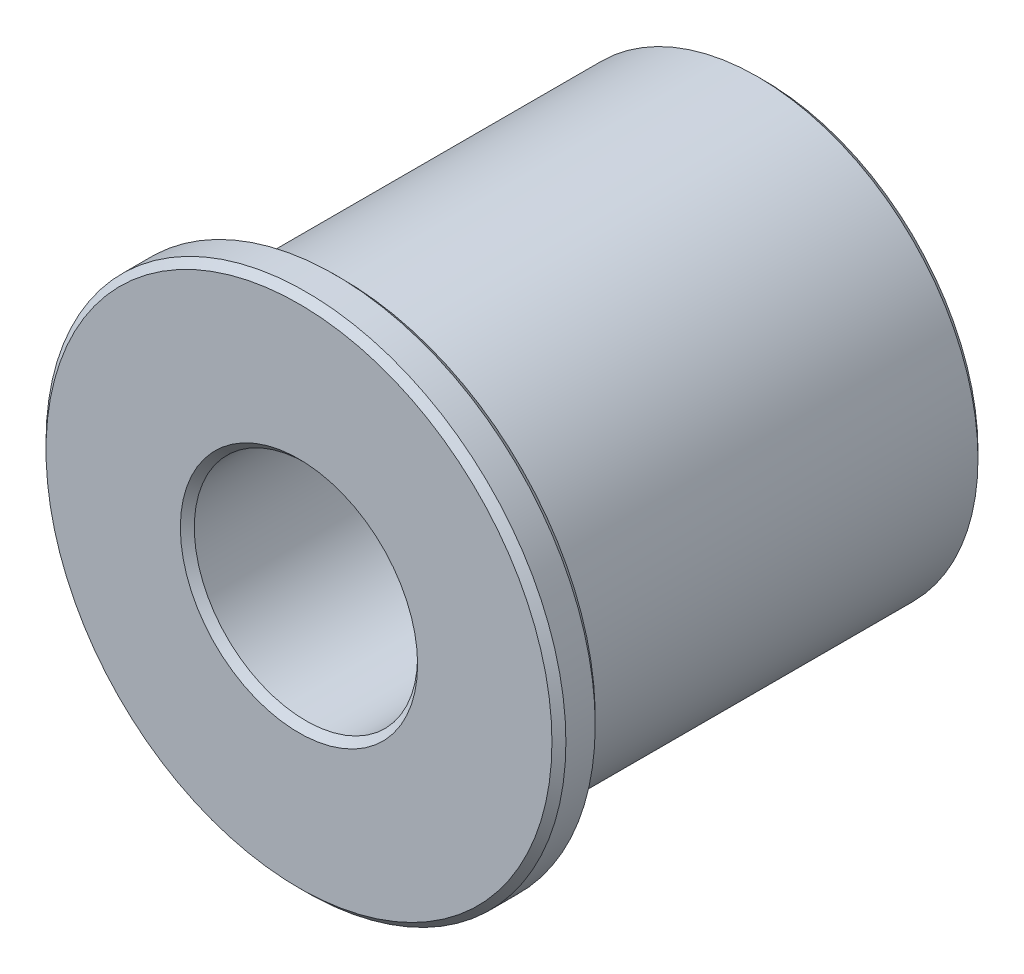
SolidWorks part; units mm, degrees
ref_plane "Front Plane" through (0, 0, 0) normal (0, 0, 1) x (1, 0, 0)
ref_plane "Top Plane" through (0, 0, 0) normal (0, 1, 0) x (1, 0, 0)
ref_plane "Right Plane" through (0, 0, 0) normal (1, 0, 0) x (0, 0, -1)
sketch "Sketch1" plane through (0, 0, 0) normal (0, 1, 0) x (1, 0, 0)
  line L0 (2.286, -10.6) -> (4.064, -10.6)
  line L1 (4.064, -10.6) -> (4.064, -16.9418)
  line L3 (8.0264, -15.367) -> (8.0264, 0)
  line L4 (8.0264, 0) -> (2.286, 0)
  line L5 (2.286, 0) -> (2.286, -10.6)
  line L6 (0, 0) -> (0, -14.6) construction
  line L7 (8.0264, -15.367) -> (9.4615, -15.367)
  line L8 (9.4615, -15.367) -> (9.4615, -16.9418)
  line L10 (4.064, -16.9418) -> (9.4615, -16.9418)
  dimension "D1" = 10.6
  dimension "D2" = 4.572
  dimension "D3" = 16.0528
  dimension "D4" = 15.367
  dimension "D5" = 8.128
  dimension "D6" = 18.923
  dimension "D7" = 1.5748
revolve "Revolve1" add sketch "Sketch1" angle 360 about L6
chamfer "Chamfer1" distance 0.254 angle 45 6 edges at (2.286, 0, 10.6) (2.286, 0, 0) (8.0264, 0, 0) (4.064, 0, 16.9418) (9.4615, 0, 15.367) (9.4615, 0, 16.9418)
